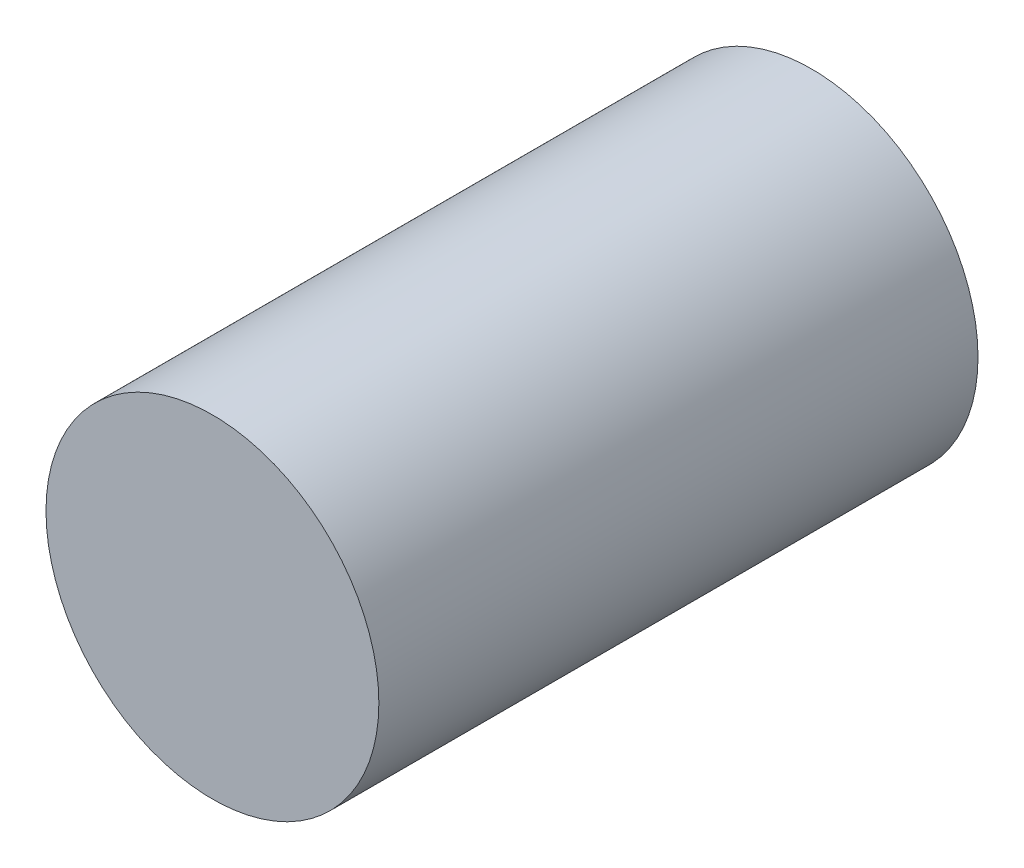
SolidWorks part; units mm, degrees
ref_plane "Alzado" through (0, 0, 0) normal (0, 0, 1) x (1, 0, 0)
ref_plane "Planta" through (0, 0, 0) normal (0, 1, 0) x (1, 0, 0)
ref_plane "Vista lateral" through (0, 0, 0) normal (1, 0, 0) x (0, 0, -1)
sketch "Croquis1" plane through (0, 0, 0) normal (0, 0, 1) x (1, 0, 0)
  circle A0 centre (0, 0) radius 5
  dimension "D1" = 10
extrude "Saliente-Extruir1" add sketch "Croquis1" along normal blind 18
